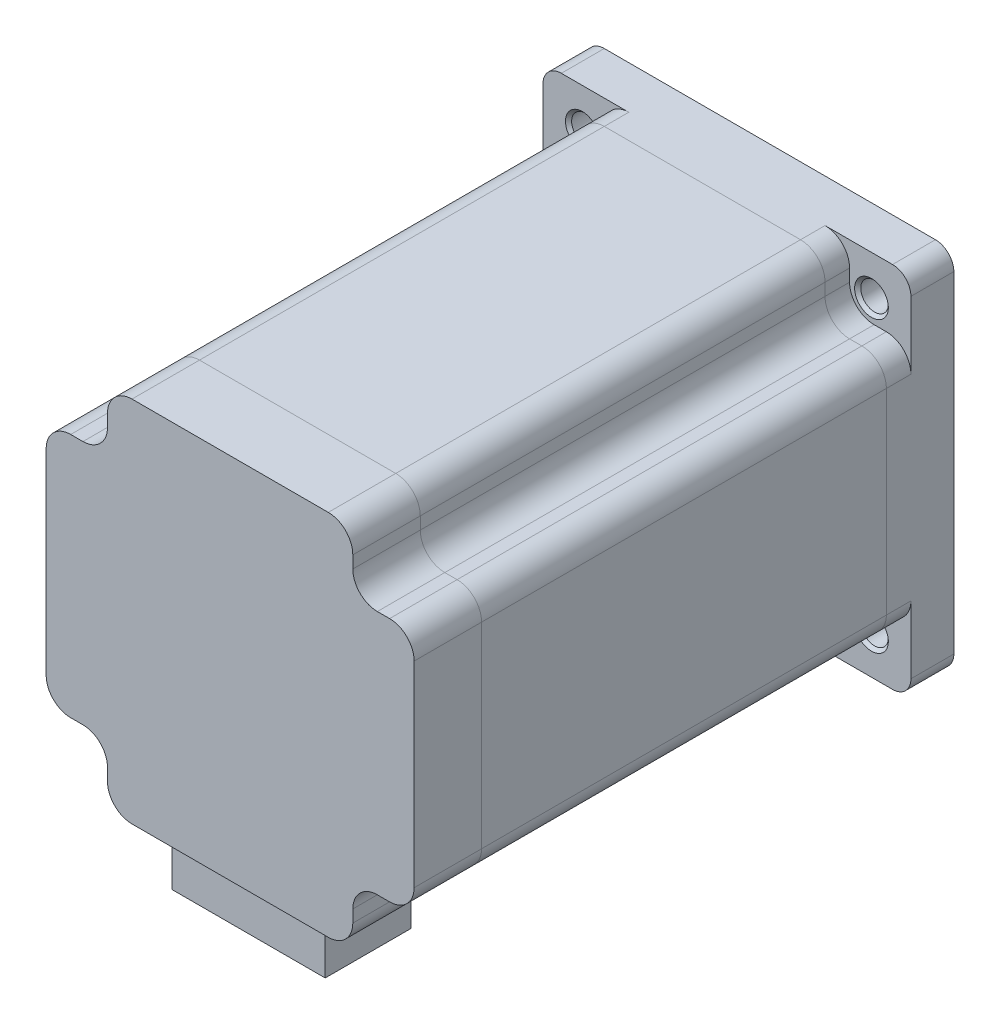
SolidWorks part; units mm, degrees
material "6061 合金"
ref_plane "前基準面" through (0, 0, 0) normal (0, 0, 1) x (1, 0, 0)
ref_plane "上基準面" through (0, 0, 0) normal (0, 1, 0) x (1, 0, 0)
ref_plane "右基準面" through (0, 0, 0) normal (1, 0, 0) x (0, 0, -1)
sketch "草圖1" plane through (0, 0, 0) normal (0, 0, 1) x (1, 0, 0)
  line L1 (-30, -30) -> (30, -30)
  line L2 (-30, -30) -> (-30, 30)
  line L3 (-30, 30) -> (30, 30)
  line L4 (30, -30) -> (30, 30)
  line L5 (-30, -30) -> (30, 30) construction
  line L6 (-30, 30) -> (30, -30) construction
  point P0 (0, 0)
  dimension "D1" = 60
  dimension "D2" = 60
extrude "填料-伸長1" add sketch "草圖1" along normal blind 11
sketch "草圖2" plane through (0, 0, 11) normal (0, 0, 1) x (1, 0, 0)
  line L1 (-30, -30) -> (30, -30)
  line L2 (-30, -30) -> (-30, 30)
  line L3 (-30, 30) -> (30, 30)
  line L4 (30, -30) -> (30, 30)
  line L5 (-30, -30) -> (30, 30) construction
  line L6 (-30, 30) -> (30, -30) construction
  point P0 (0, 0)
extrude "填料-伸長2" add sketch "草圖2" along normal blind 66 separate body
sketch "草圖3" plane through (0, 0, 77) normal (0, 0, 1) x (1, 0, 0)
  line L1 (-30, -30) -> (30, -30)
  line L2 (-30, -30) -> (-30, 30)
  line L3 (-30, 30) -> (30, 30)
  line L4 (30, -30) -> (30, 30)
  line L5 (-30, -30) -> (30, 30) construction
  line L6 (-30, 30) -> (30, -30) construction
  point P0 (0, 0)
extrude "填料-伸長3" add sketch "草圖3" along normal blind 11 separate body
sketch "草圖4" plane through (0, 0, 0) normal (0, 0, -1) x (-1, 0, 0)
  circle A0 centre (0, 0) radius 19.05
  dimension "D1" = 38.1
extrude "填料-伸長4" add sketch "草圖4" along normal blind 1.6
sketch "草圖5" plane through (0, 0, -1.6) normal (0, 0, -1) x (-1, 0, 0)
  circle A0 centre (0, 0) radius 5
  dimension "D1" = 10
extrude "除料-伸長1" cut sketch "草圖5" against normal blind 5
sketch "草圖6" plane through (0, 0, 3.4) normal (0, 0, -1) x (-1, 0, 0)
  circle A0 centre (0, 0) radius 4
  dimension "D1" = 8
extrude "填料-伸長5" add sketch "草圖6" along normal offset from surface (27.4 mm away) 24 separate body up to face at (-19.05, 0, 0) offset beyond the face yes
sketch "草圖7" plane through (0, 0, -24) normal (0, 0, -1) x (-1, 0, 0)
  line L0 (-1.9365, 3.5) -> (1.9365, 3.5)
  arc A0 (-1.9365, 3.5) -> (1.9365, 3.5) centre (0, 0) cw
  circle A1 centre (0, 0) radius 4 construction
  dimension "D1" = 3.5
extrude "除料-伸長2" cut sketch "草圖7" against normal blind 20
sketch "草圖8" plane through (0, 0, 88) normal (0, 0, 1) x (1, 0, 0)
  line L0 (30, 30) -> (-30, 30) construction
  line L1 (30, 30) -> (20, 30)
  line L2 (30, 30) -> (30, 20)
  line L3 (30, 20) -> (20, 20)
  line L4 (20, 30) -> (20, 20)
  line L5 (30, 30) -> (20, 20) construction
  line L6 (30, 20) -> (20, 30) construction
  point P4 (25, 25)
  dimension "D1" = 10
  dimension "D2" = 10
extrude "除料-伸長3" cut sketch "草圖8" against normal offset from surface (81 mm away) 7 up to face at (-19.05, 0, 0)
pattern_circular "環狀複製排列1" count 4 over 360 about axis through (0, 0, 0) along (0, 0, 1) of "除料-伸長3"
hole_wizard "M4 餘隙孔1" positions "草圖10" profile "草圖11" hole size "M4" standard "Ansi Metric" end condition through all
sketch "草圖10" plane through (0, 0, 7) normal (0, 0, 1) x (1, 0, 0)
  line L9 (-23.57, -23.57) -> (23.57, -23.57) construction
  line L10 (-23.57, -23.57) -> (-23.57, 23.57) construction
  line L11 (-23.57, 23.57) -> (23.57, 23.57) construction
  line L12 (23.57, -23.57) -> (23.57, 23.57) construction
  line L13 (-23.57, -23.57) -> (23.57, 23.57) construction
  line L14 (-23.57, 23.57) -> (23.57, -23.57) construction
  point P32 (23.57, 23.57)
  point P65 (-23.57, -23.57)
  point P66 (-23.57, 23.57)
  point P67 (23.57, -23.57)
  dimension "D1" = 47.14
  dimension "D2" = 47.14
sketch "草圖11" plane through (23.57, 23.57, 7) normal (1, 0, 0) x (0, -1, 0)
  line L0 (0, 0) -> (0, 31)
  line L1 (0, 31) -> (2.25, 31)
  line L2 (2.25, 31) -> (2.25, 0)
  line L5 (2.25, 0) -> (0, 0)
  line L11 (0, -6.35) -> (0, 107.95) construction
  dimension "貫穿孔直徑" = 4.5
  dimension "貫穿孔深度" = 31
chamfer "導角1" distance 0.5 angle 45 8 edges at (-21.32, 23.57, 7) (-25.82, 23.57, 0) (-21.32, -23.57, 7) (-25.82, -23.57, 0) (25.82, -23.57, 7) (21.32, -23.57, 0) (25.82, 23.57, 7) (21.32, 23.57, 0)
fillet "圓角1" radius 3 4 edges at (30, 30, 3.5) (30, -30, 3.5) (-30, -30, 3.5) (-30, 30, 3.5)
fillet "圓角2" radius 4 12 edges at (20, 20, 9) (30, 20, 9) (20, 30, 9) (30, -20, 9) (20, -20, 9) (20, -30, 9) (-20, -30, 9) (-20, -20, 9) (-30, -20, 9) (-30, 20, 9) (-20, 20, 9) (-20, 30, 9)
fillet "圓角3" radius 4 12 edges at (20, 20, 44) (30, 20, 44) (20, 30, 44) (30, -20, 44) (20, -20, 44) (20, -30, 44) (-20, -30, 44) (-20, -20, 44) (-30, -20, 44) (-30, 20, 44) (-20, 20, 44) (-20, 30, 44)
fillet "圓角4" radius 4 12 edges at (20, 20, 82.5) (30, 20, 82.5) (20, 30, 82.5) (30, -20, 82.5) (20, -20, 82.5) (20, -30, 82.5) (-20, -30, 82.5) (-20, -20, 82.5) (-30, -20, 82.5) (-30, 20, 82.5) (-20, 20, 82.5) (-20, 30, 82.5)
sketch "草圖12" plane through (0, -30, 0) normal (0, -1, 0) x (1, 0, 0)
  line L0 (0, 88) -> (0, 78) construction
  line L1 (-16, 88) -> (16, 88) construction
  line L3 (-12.5, 85) -> (12.5, 85)
  line L4 (-12.5, 85) -> (-12.5, 71)
  line L5 (-12.5, 71) -> (12.5, 71)
  line L6 (12.5, 85) -> (12.5, 71)
  line L7 (-12.5, 85) -> (12.5, 71) construction
  line L8 (-12.5, 71) -> (12.5, 85) construction
  dimension "D1" = 3
  dimension "D2" = 14
  dimension "D3" = 25
extrude "填料-伸長6" add sketch "草圖12" along normal blind 9 separate body
sketch "草圖13" plane through (0, 0, 71) normal (0, 0, -1) x (-1, 0, 0)
  line L0 (0, -30) -> (0, -39) construction
  line L2 (12.5, -30) -> (-12.5, -30) construction
  line L3 (12.5, -39) -> (-12.5, -39) construction
  line L4 (0, -34.5) -> (1.5, -34.5) construction
  circle A1 centre (1.5, -34.5) radius 0.8
  point P9 (0, -34.5)
  dimension "D2" = 1.6
  dimension "D1" = 1.5
extrude "填料-伸長7" add sketch "草圖13" along normal blind 10 separate body
pattern_linear "直線複製排列1" count 5 spacing 3 along (1, 0, 0) count 4 spacing 3 along (-1, 0, 0) of "填料-伸長7"
